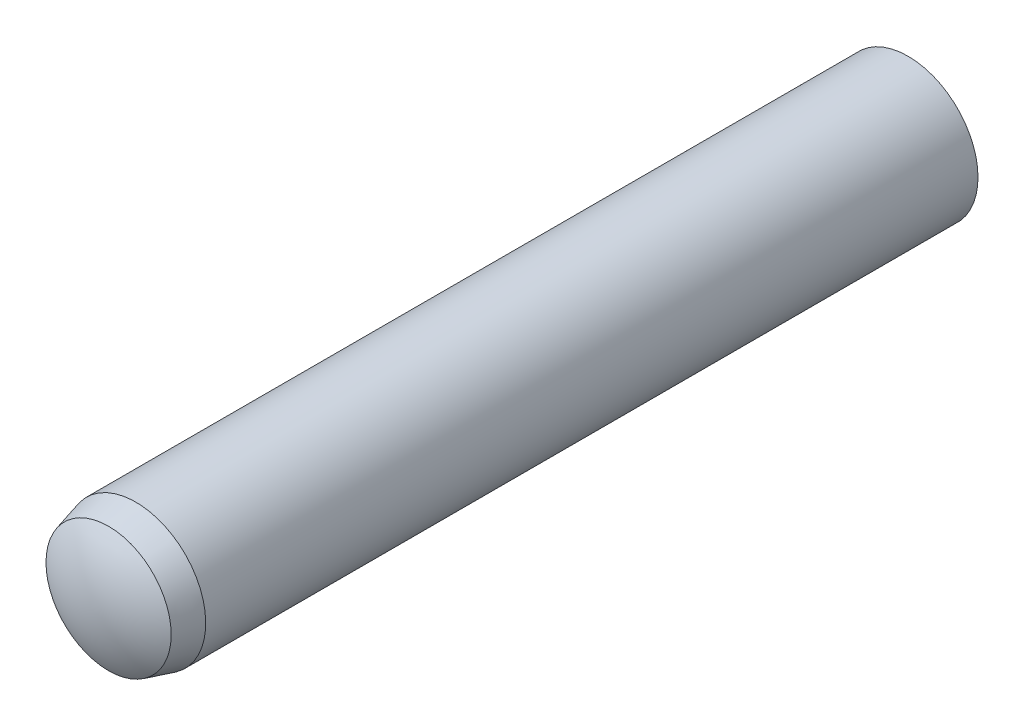
SolidWorks part; units mm, degrees
ref_plane "Front Plane" through (0, 0, 0) normal (0, 0, 1) x (1, 0, 0)
ref_plane "Top Plane" through (0, 0, 0) normal (0, 1, 0) x (1, 0, 0)
ref_plane "Right Plane" through (0, 0, 0) normal (1, 0, 0) x (0, 0, -1)
sketch "Sketch1" plane through (0, 0, 0) normal (0, 0, 1) x (1, 0, 0)
  circle A0 centre (0, 0) radius 1
  point P3 (0, 1)
  dimension "Diameter" = 2
sketch "Sketch2" plane through (0, 0, 0) normal (1, 0, 0) x (0, 0, -1)
  line L0 (-6, 0) -> (6, 0) construction
  line L1 (-6, 0) -> (-6, 1) construction
  line L2 (-6, 1) -> (6, 1)
  line L3 (6, 1) -> (6, 0) construction
  line L4 (-5.74, 0.8955) -> (-5.35, 1)
  arc A0 (-6, 0) -> (-5.74, 0.8955) centre (-4.3278, 0) cw
  arc A1 (6, 0) -> (5.7, 1) centre (4.1833, 0) ccw
  point P2 (0, 0)
  point P11 (-4, 0)
  point P13 (4, 0)
  dimension "Length" = 12
  dimension "D1" = 15
  dimension "D2" = 0.3
  dimension "D3" = 0.65
  dimension "D4" = 0.39
  dimension "D5" = 2
  dimension "D6" = 2
sketch "Sketch3" plane through (0, 0, 0) normal (1, 0, 0) x (0, 0, -1)
  line L0 (-6, 0) -> (6, 0) construction
  line L1 (-5.74, 0.8955) -> (-5.35, 1) construction
  line L2 (-6, 0) -> (6, 0)
  line L3 (-5.74, 0.8955) -> (-5.35, 1)
  line L4 (-5.35, 1) -> (5.7, 1)
  arc A0 (6, 0) -> (5.7, 1) centre (4.1833, 0) ccw construction
  arc A1 (-5.74, 0.8955) -> (-6, 0) centre (-4.3278, 0) ccw construction
  arc A2 (6, 0) -> (5.7, 1) centre (4.1833, 0) ccw
  arc A3 (-5.74, 0.8955) -> (-6, 0) centre (-4.3278, 0) ccw
revolve "Revolve1" add sketch "Sketch3" angle 360 about L2
equation "\"D2@Sketch2\" = \"Diameter@Sketch1\" * .15"
equation "\"D3@Sketch2\" = \"Diameter@Sketch1\" * .325"
equation "\"D4@Sketch2\" = \"D3@Sketch2\" * .6"
equation "\"D5@Sketch2\"=\"Diameter@Sketch1\""
equation "\"D6@Sketch2\"=\"D5@sketch2\""
